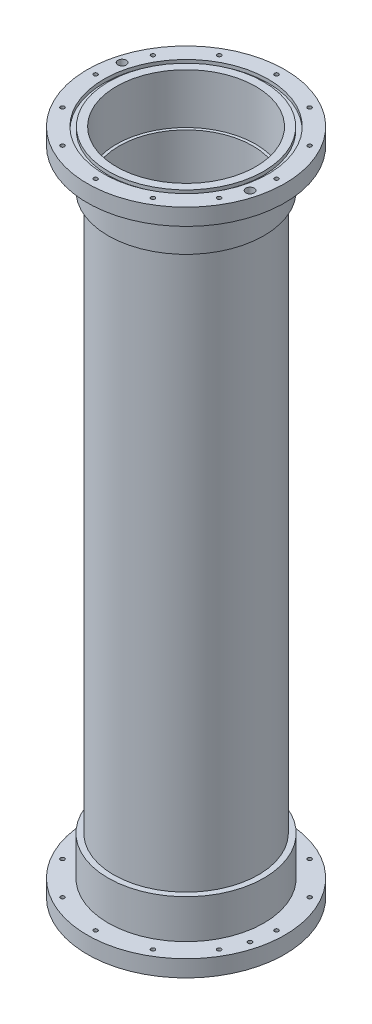
SolidWorks part; units mm, degrees
material "7075-T6 (SN)"
ref_plane "Front Plane" through (0, 0, 0) normal (0, 0, 1) x (1, 0, 0)
ref_plane "Top Plane" through (0, 0, 0) normal (0, 1, 0) x (1, 0, 0)
ref_plane "Right Plane" through (0, 0, 0) normal (1, 0, 0) x (0, 0, -1)
sketch "Sketch2" plane through (0, 0, 0) normal (0, 1, 0) x (1, 0, 0)
  circle A0 centre (0, 0) radius 38.1
  circle A1 centre (0, 0) radius 41.275
  dimension "D1" = 82.55
  dimension "D2" = 76.2
extrude "Base Cylinder" add sketch "Sketch2" along normal blind 381
sketch "Sketch3" plane through (0, 0, 0) normal (0, -1, 0) x (1, 0, 0)
  circle A0 centre (0, 0) radius 38.1
  circle A1 centre (0, 0) radius 56.3562
  dimension "D1" = 112.7125
extrude "Aft Flange" add sketch "Sketch3" against normal blind 9.525
sketch "Sketch34" plane through (0, 0, 0) normal (0, -1, 0) x (1, 0, 0)
  circle A0 centre (0, 0) radius 39.75
  dimension "D1" = 79.5
extrude "TemperatureInsert" cut sketch "Sketch34" against normal blind 28.575
sketch "Sketch6" plane through (0, 0, 0) normal (0, -1, 0) x (1, 0, 0)
  circle A0 centre (0, 0) radius 46.9011
  circle A1 centre (0, 0) radius 44.2849
  dimension "D1" = 93.8022
  dimension "D2" = 88.5698
extrude "Aft O-Ring" cut sketch "Sketch6" against normal blind 1.9812
sketch "Sketch33" plane through (0, 9.525, 0) normal (0, 1, 0) x (1, 0, 0)
  circle A0 centre (0, 0) radius 41.275
  circle A1 centre (0, 0) radius 44.45
  dimension "D1" = 82.55
  dimension "D2" = 88.9
extrude "CriticalBoss" add sketch "Sketch33" along normal blind 22.225
sketch "Sketch For Bolt Holes" plane through (0, 0, 0) normal (0, -1, 0) x (1, 0, 0)
  circle A0 centre (-51.6255, 0) radius 1.5875
  circle A1 centre (-44.709, 25.8128) radius 1.5875
  circle A2 centre (-25.8128, 44.709) radius 1.5875
  circle A3 centre (0, 51.6255) radius 1.5875
  circle A4 centre (25.8127, 44.709) radius 1.5875
  circle A5 centre (44.709, 25.8128) radius 1.5875
  circle A6 centre (51.6255, 0) radius 1.5875
  circle A7 centre (44.709, -25.8127) radius 1.5875
  circle A8 centre (25.8128, -44.709) radius 1.5875
  circle A9 centre (0, -51.6255) radius 1.5875
  circle A10 centre (-25.8127, -44.709) radius 1.5875
  circle A11 centre (-44.709, -25.8128) radius 1.5875
  point P36 (0, 0)
  dimension "D2" = 3.175
  dimension "D1" = 51.6255
  dimension "D3" = 12
hole_wizard "Bolt Circle" positions "Sketch8" profile "Sketch9" hole size "#4-40" standard "ANSI Inch" end condition up to next
sketch "Sketch8" plane through (0, 0, 0) normal (0, -1, 0) x (-1, 0, 0)
  point P0 (-25.8127, -44.709)
  point P3 (-44.709, -25.8128)
  point P6 (-51.6255, 0)
  point P9 (-44.709, 25.8127)
  point P12 (-25.8128, 44.709)
  point P15 (0, 51.6255)
  point P18 (25.8127, 44.709)
  point P21 (44.709, 25.8128)
  point P24 (51.6255, 0)
  point P27 (44.709, -25.8128)
  point P30 (25.8128, -44.709)
  point P33 (0, -51.6255)
  point P36 (-25.8127, -44.709)
  point P38 (-44.709, -25.8128)
  point P40 (-51.6255, 0)
sketch "Sketch9" plane through (25.8127, 0, 44.709) normal (1, 0, 0) x (0, 0, -1)
  line L0 (0, 0) -> (0, 381)
  line L1 (0, 381) -> (1.1303, 381)
  line L2 (1.1303, 381) -> (1.1303, 0)
  line L5 (1.1303, 0) -> (0, 0)
  line L11 (0, -6.35) -> (0, 107.95) construction
  dimension "Thru Hole Dia." = 2.2606
  dimension "Thru Hole Depth" = 381
sketch "Dowel Hole Sketch" plane through (0, 0, 0) normal (0, -1, 0) x (1, 0, 0)
  line L0 (0, 0) -> (-51.6255, 0) construction
  line L1 (0, 0) -> (-49.8664, -13.3617) construction
  line L2 (0, 0) -> (0, -51.6255) construction
  line L3 (0, 0) -> (49.8664, 13.3617) construction
  circle A0 centre (0, 0) radius 51.6255
  circle A1 centre (-49.8664, -13.3617) radius 4.6172
  circle A2 centre (49.8664, 13.3617) radius 3.4532
  dimension "D1" = 15
hole_wizard "Hole1" positions "Sketch14" profile "Sketch12" legacy end condition up to next
sketch "Sketch14" plane through (0, 0, 0) normal (0, -1, 0) x (-1, 0, 0)
  point P0 (49.8664, 13.3617)
  point P3 (-49.8664, -13.3617)
sketch "Sketch12" plane through (-49.8664, 0, -13.3617) normal (1, 0, 0) x (0, 0, -1)
  line L0 (0, 0) -> (0, 381)
  line L1 (0, 381) -> (1.1906, 381)
  line L2 (1.1906, 381) -> (1.1906, 4.7625)
  line L3 (1.1906, 4.7625) -> (2.3813, 4.7625)
  line L4 (2.3813, 4.7625) -> (2.3813, 0)
  line L5 (2.3813, 0) -> (0, 0)
  line L6 (0, 110) -> (0, -10) construction
  dimension "Diameter" = 2.3813
  dimension "Depth" = 381
  dimension "C-Bore Diameter" = 4.7625
  dimension "C-Bore Depth" = 4.7625
ref_plane "Hoop Mid-Plane" through (0, 190.5, 0) normal (0, 1, 0) x (1, 0, 0)
ref_plane "PressureTapHolePlane" through (0, 0, 44.45) normal (0, 0, 1) x (1, 0, 0)
ref_plane "TemperatureTapPlane" through (0, 0, -44.45) normal (0, 0, 1) x (1, 0, 0)
sketch "ThermoHole" plane through (0, 0, -44.45) normal (0, 0, 1) x (1, 0, 0)
  line L0 (-56.3562, 0) -> (56.3562, 0) construction
  circle A0 centre (0, 19.05) radius 3.175
  dimension "D1" = 19.05
  dimension "D2" = 6.35
sketch "Sketch35" plane through (0, 0, 44.45) normal (0, 0, 1) x (1, 0, 0)
  line L0 (-56.3562, 0) -> (56.3562, 0) construction
  circle A0 centre (0, 19.05) radius 1.5875
  dimension "D1" = 19.05
  dimension "D2" = 3.175
extrude "Pressure Tap Aft Big" [suppressed] cut sketch "Sketch35" against normal blind 2.3813
sketch "Sketch41" [suppressed] plane through (0, 0, 42.0687) normal (0, 0, 1) x (1, 0, 0)
  circle A0 centre (0, 19.05) radius 0.1984
extrude "Pressure Tap Aft Small" [suppressed] cut sketch "Sketch41" against normal up to next
hole_wizard "1/8 NPT Tapped ThermocoupleHole" [suppressed] positions "Sketch43" profile "Sketch44" size "1/8" standard "ANSI Inch"
sketch "Sketch43" plane through (0, 0, -44.45) normal (0, 0, 1) x (1, 0, 0)
  point P0 (0, 19.05)
sketch "Sketch44" plane through (0, 19.05, -44.45) normal (1, 0, 0) x (0, 1, 0)
  line L0 (0, 0) -> (0, 14.2175)
  line L1 (4.2164, 11.684) -> (0, 14.2175)
  line L2 (-4.2164, 11.684) -> (0, 14.2175) construction
  line L3 (4.2164, 11.684) -> (4.2164, 6.858)
  line L4 (4.2164, 6.858) -> (4.9362, 6.858)
  line L5 (4.9362, 6.858) -> (5.1415, 0)
  line L6 (-4.9362, 6.858) -> (-5.1415, 0) construction
  line L7 (5.1415, 0) -> (0, 0)
  line L8 (0, -6.35) -> (0, 107.95) construction
  line L11 (-4.2164, 6.858) -> (-4.9362, 6.858) construction
  dimension "Tap Drill Dia." = 8.4328
  dimension "Tap Drill Depth" = 11.684
  dimension "Thread Dia." = 10.283
  dimension "Thread Angle" = 3.43
  dimension "Thread Depth" = 6.858
  dimension "Drill Angle" = 118
mirror "Mirror1" about plane through (0, 190.5, 0) normal (0, 1, 0) of "Aft Flange", "TemperatureInsert", "Aft O-Ring", "CriticalBoss", "Bolt Circle", "Hole1"
